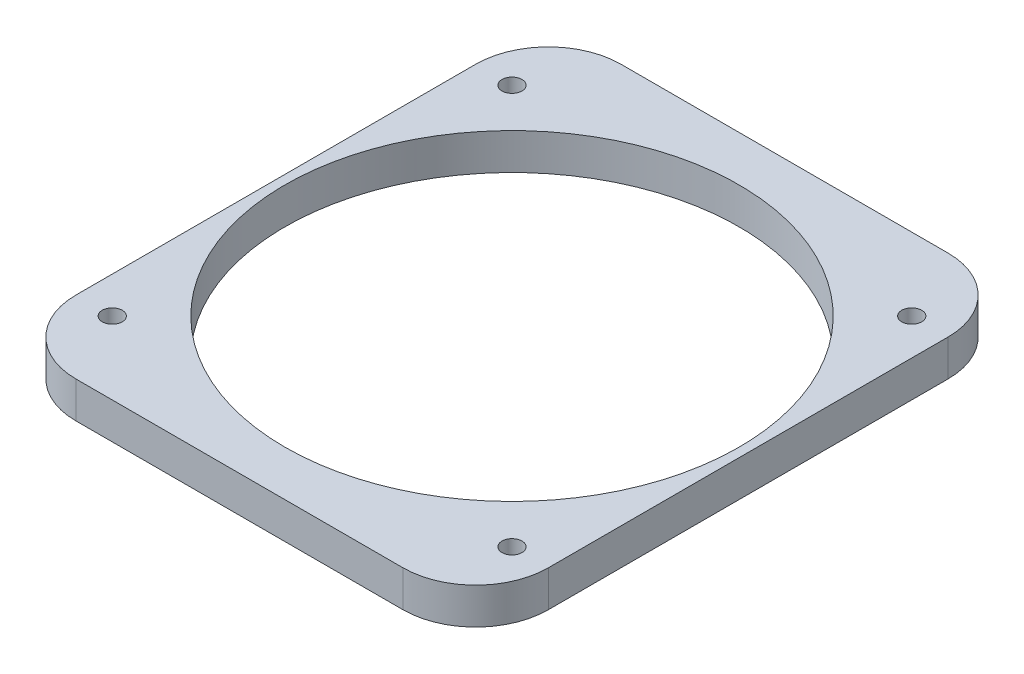
SolidWorks part; units mm, degrees
ref_plane "Front Plane" through (0, 0, 0) normal (0, 0, 1) x (1, 0, 0)
ref_plane "Top Plane" through (0, 0, 0) normal (0, 1, 0) x (1, 0, 0)
ref_plane "Right Plane" through (0, 0, 0) normal (1, 0, 0) x (0, 0, -1)
sketch "Sketch1" plane through (0, 0, 0) normal (0, 1, 0) x (1, 0, 0)
  line L1 (41.275, -47.625) -> (-41.275, -47.625)
  line L2 (41.275, -47.625) -> (41.275, 47.625)
  line L3 (41.275, 47.625) -> (-41.275, 47.625)
  line L4 (-41.275, -47.625) -> (-41.275, 47.625)
  line L5 (41.275, -47.625) -> (-41.275, 47.625) construction
  line L6 (41.275, 47.625) -> (-41.275, -47.625) construction
  line L7 (34.925, -34.925) -> (-34.925, -34.925) construction
  line L8 (34.925, -34.925) -> (34.925, 34.925) construction
  line L9 (34.925, 34.925) -> (-34.925, 34.925) construction
  line L10 (-34.925, -34.925) -> (-34.925, 34.925) construction
  line L11 (34.925, -34.925) -> (-34.925, 34.925) construction
  line L12 (34.925, 34.925) -> (-34.925, -34.925) construction
  circle A0 centre (0, 0) radius 38.1
  circle A1 centre (-34.925, 34.925) radius 1.75
  circle A2 centre (-34.925, -34.925) radius 1.75
  circle A3 centre (34.925, -34.925) radius 1.75
  circle A4 centre (34.925, 34.925) radius 1.75
  point P0 (0, 0)
  dimension "D3" = 76.2
  dimension "D5" = 3.5
  dimension "D1" = 82.55
  dimension "D2" = 95.25
  dimension "D4" = 69.85
extrude "Boss-Extrude1" add sketch "Sketch1" along normal blind 6.35
fillet "Fillet1" radius 12.7 4 edges at (-41.275, 3.175, -47.625) (41.275, 3.175, -47.625) (41.275, 3.175, 47.625) (-41.275, 3.175, 47.625)
sketch "Sketch2" plane through (0, 6.35, 0) normal (0, 1, 0) x (1, 0, 0)
  circle A0 centre (0, 0) radius 38.1
  circle A1 centre (0, 0) radius 38.1 construction
  circle A2 centre (0, 0) radius 39.6875
  dimension "D1" = 1.5875
extrude "Cut-Extrude1" cut sketch "Sketch2" against normal through all
